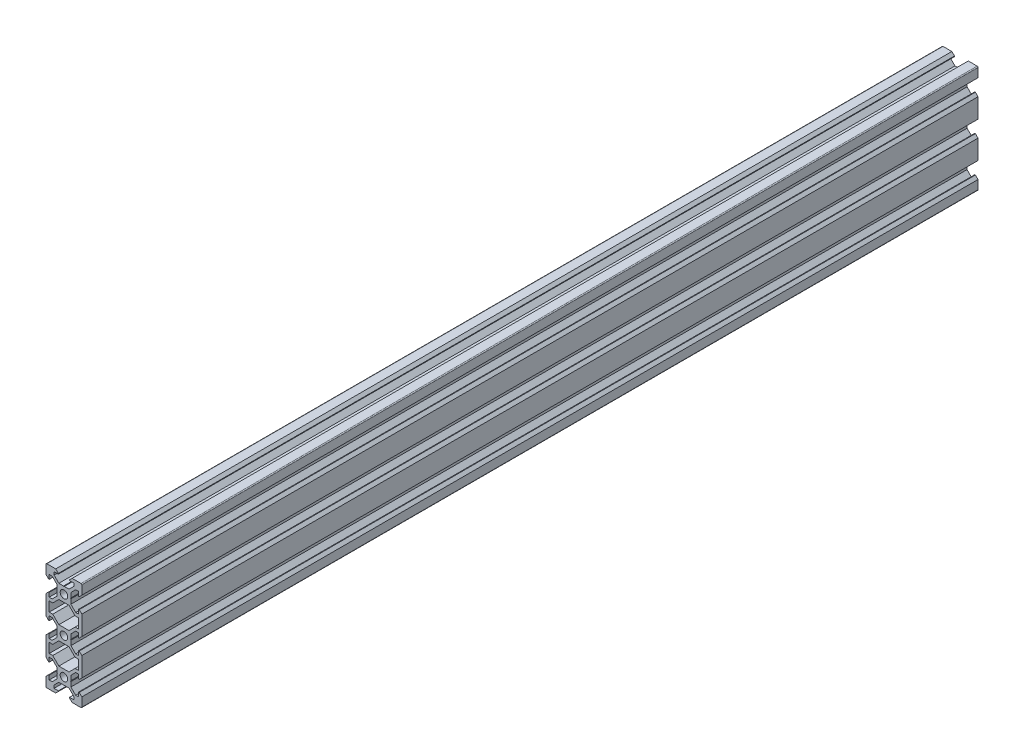
SolidWorks part; units mm, degrees
ref_plane "Front Plane" through (0, 0, 0) normal (0, 0, 1) x (1, 0, 0)
ref_plane "Top Plane" through (0, 0, 0) normal (0, 1, 0) x (1, 0, 0)
ref_plane "Right Plane" through (0, 0, 0) normal (1, 0, 0) x (0, 0, -1)
sketch "Sketch1" plane through (0, 0, 0) normal (0, 0, 1) x (1, 0, 0)
  line B0 (-8.2, -32.7) -> (-6.2393, -32.7)
  line B1 (-6.2393, -32.7) -> (-2.8393, -36.1)
  line B2 (-2.8393, -36.1) -> (2.8393, -36.1)
  line B3 (6.2393, -32.7) -> (2.8393, -36.1)
  line B4 (8.2, -32.7) -> (6.2393, -32.7)
  line B5 (8.2, -32.7) -> (8.2, -27.3)
  line B6 (8.2, -27.3) -> (6.2393, -27.3)
  line B7 (6.2393, -27.3) -> (2.8393, -23.9)
  line B8 (-2.8393, -23.9) -> (2.8393, -23.9)
  line B9 (-6.2393, -27.3) -> (-2.8393, -23.9)
  line B10 (-8.2, -27.3) -> (-6.2393, -27.3)
  line B11 (-8.2, -32.7) -> (-8.2, -27.3)
  line B12 (-8.2, -12.7) -> (-6.2393, -12.7)
  line B13 (-6.2393, -12.7) -> (-2.8393, -16.1)
  line B14 (-2.8393, -16.1) -> (2.8393, -16.1)
  line B15 (6.2393, -12.7) -> (2.8393, -16.1)
  line B16 (8.2, -12.7) -> (6.2393, -12.7)
  line B17 (8.2, -12.7) -> (8.2, -7.3)
  line B18 (8.2, -7.3) -> (6.2393, -7.3)
  line B19 (6.2393, -7.3) -> (2.8393, -3.9)
  line B20 (-2.8393, -3.9) -> (2.8393, -3.9)
  line B21 (-6.2393, -7.3) -> (-2.8393, -3.9)
  line B22 (-8.2, -7.3) -> (-6.2393, -7.3)
  line B23 (-8.2, -12.7) -> (-8.2, -7.3)
  line B24 (3.69, 0) -> (3.9, -0.21)
  line B25 (3.9, -0.21) -> (3.9, -2.8393)
  line B26 (3.9, -2.8393) -> (6.5607, -5.5)
  line B27 (6.5607, -5.5) -> (8.2, -5.5)
  line B28 (8.2, -5.5) -> (8.2, -3.125)
  line B29 (8.2, -3.125) -> (8.545, -3.125)
  line B30 (8.545, -3.125) -> (10, -4.58)
  line B31 (10, -15.42) -> (10, -4.58)
  line B32 (8.545, -16.875) -> (10, -15.42)
  line B33 (8.2, -16.875) -> (8.545, -16.875)
  line B34 (8.2, -14.5) -> (8.2, -16.875)
  line B35 (6.5607, -14.5) -> (8.2, -14.5)
  line B36 (3.9, -17.1607) -> (6.5607, -14.5)
  line B37 (3.9, -19.79) -> (3.9, -17.1607)
  line B38 (3.69, -20) -> (3.9, -19.79)
  line B39 (3.69, -20) -> (3.9, -20.21)
  line B40 (3.9, -20.21) -> (3.9, -22.8393)
  line B41 (3.9, -22.8393) -> (6.5607, -25.5)
  line B42 (6.5607, -25.5) -> (8.2, -25.5)
  line B43 (8.2, -25.5) -> (8.2, -23.125)
  line B44 (8.2, -23.125) -> (8.545, -23.125)
  line B45 (8.545, -23.125) -> (10, -24.58)
  line B46 (10, -35.42) -> (10, -24.58)
  line B47 (8.545, -36.875) -> (10, -35.42)
  line B48 (8.2, -36.875) -> (8.545, -36.875)
  line B49 (8.2, -34.5) -> (8.2, -36.875)
  line B50 (6.5607, -34.5) -> (8.2, -34.5)
  line B51 (3.9, -37.1607) -> (6.5607, -34.5)
  line B52 (3.9, -39.79) -> (3.9, -37.1607)
  line B53 (3.69, -40) -> (3.9, -39.79)
  line B54 (3.69, -40) -> (3.9, -40.21)
  line B55 (3.9, -40.21) -> (3.9, -42.8393)
  line B56 (3.9, -42.8393) -> (6.5607, -45.5)
  line B57 (6.5607, -45.5) -> (8.2, -45.5)
  line B58 (8.2, -45.5) -> (8.2, -43.125)
  line B59 (8.2, -43.125) -> (8.545, -43.125)
  line B60 (8.545, -43.125) -> (10, -44.58)
  line B61 (10, -49.5) -> (10, -44.58)
  arc B62 (9.5, -50) -> (10, -49.5) centre (9.5, -49.5) ccw
  line B63 (9.5, -50) -> (4.58, -50)
  line B64 (3.125, -48.545) -> (4.58, -50)
  line B65 (3.125, -48.2) -> (3.125, -48.545)
  line B66 (5.5, -48.2) -> (3.125, -48.2)
  line B67 (5.5, -46.5607) -> (5.5, -48.2)
  line B68 (2.8393, -43.9) -> (5.5, -46.5607)
  line B69 (0.21, -43.9) -> (2.8393, -43.9)
  line B70 (0, -43.69) -> (0.21, -43.9)
  line B71 (0, -43.69) -> (-0.21, -43.9)
  line B72 (-0.21, -43.9) -> (-2.8393, -43.9)
  line B73 (-2.8393, -43.9) -> (-5.5, -46.5607)
  line B74 (-5.5, -46.5607) -> (-5.5, -48.2)
  line B75 (-5.5, -48.2) -> (-3.125, -48.2)
  line B76 (-3.125, -48.2) -> (-3.125, -48.545)
  line B77 (-3.125, -48.545) -> (-4.58, -50)
  line B78 (-4.58, -50) -> (-9.5, -50)
  arc B79 (-10, -49.5) -> (-9.5, -50) centre (-9.5, -49.5) ccw
  line B80 (-10, -49.5) -> (-10, -44.58)
  line B81 (-8.545, -43.125) -> (-10, -44.58)
  line B82 (-8.2, -43.125) -> (-8.545, -43.125)
  line B83 (-8.2, -45.5) -> (-8.2, -43.125)
  line B84 (-6.5607, -45.5) -> (-8.2, -45.5)
  line B85 (-3.9, -42.8393) -> (-6.5607, -45.5)
  line B86 (-3.9, -40.21) -> (-3.9, -42.8393)
  line B87 (-3.69, -40) -> (-3.9, -40.21)
  line B88 (-3.69, -40) -> (-3.9, -39.79)
  line B89 (-3.9, -39.79) -> (-3.9, -37.1607)
  line B90 (-3.9, -37.1607) -> (-6.5607, -34.5)
  line B91 (-6.5607, -34.5) -> (-8.2, -34.5)
  line B92 (-8.2, -34.5) -> (-8.2, -36.875)
  line B93 (-8.2, -36.875) -> (-8.545, -36.875)
  line B94 (-8.545, -36.875) -> (-10, -35.42)
  line B95 (-10, -35.42) -> (-10, -24.58)
  line B96 (-8.545, -23.125) -> (-10, -24.58)
  line B97 (-8.2, -23.125) -> (-8.545, -23.125)
  line B98 (-8.2, -25.5) -> (-8.2, -23.125)
  line B99 (-6.5607, -25.5) -> (-8.2, -25.5)
  line B100 (-3.9, -22.8393) -> (-6.5607, -25.5)
  line B101 (-3.9, -20.21) -> (-3.9, -22.8393)
  line B102 (-3.69, -20) -> (-3.9, -20.21)
  line B103 (-3.69, -20) -> (-3.9, -19.79)
  line B104 (-3.9, -19.79) -> (-3.9, -17.1607)
  line B105 (-3.9, -17.1607) -> (-6.5607, -14.5)
  line B106 (-6.5607, -14.5) -> (-8.2, -14.5)
  line B107 (-8.2, -14.5) -> (-8.2, -16.875)
  line B108 (-8.2, -16.875) -> (-8.545, -16.875)
  line B109 (-8.545, -16.875) -> (-10, -15.42)
  line B110 (-10, -15.42) -> (-10, -4.58)
  line B111 (-8.545, -3.125) -> (-10, -4.58)
  line B112 (-8.2, -3.125) -> (-8.545, -3.125)
  line B113 (-8.2, -5.5) -> (-8.2, -3.125)
  line B114 (-6.5607, -5.5) -> (-8.2, -5.5)
  line B115 (-3.9, -2.8393) -> (-6.5607, -5.5)
  line B116 (-3.9, -0.21) -> (-3.9, -2.8393)
  line B117 (-3.69, 0) -> (-3.9, -0.21)
  line B118 (-3.69, 0) -> (-3.9, 0.21)
  line B119 (-3.9, 0.21) -> (-3.9, 2.8393)
  line B120 (-3.9, 2.8393) -> (-6.5607, 5.5)
  line B121 (-6.5607, 5.5) -> (-8.2, 5.5)
  line B122 (-8.2, 5.5) -> (-8.2, 3.125)
  line B123 (-8.2, 3.125) -> (-8.545, 3.125)
  line B124 (-8.545, 3.125) -> (-10, 4.58)
  line B125 (-10, 4.58) -> (-10, 9.5)
  arc B126 (-9.5, 10) -> (-10, 9.5) centre (-9.5, 9.5) ccw
  line B127 (-4.58, 10) -> (-9.5, 10)
  line B128 (-3.125, 8.545) -> (-4.58, 10)
  line B129 (-3.125, 8.2) -> (-3.125, 8.545)
  line B130 (-5.5, 8.2) -> (-3.125, 8.2)
  line B131 (-5.5, 6.5607) -> (-5.5, 8.2)
  line B132 (-2.8393, 3.9) -> (-5.5, 6.5607)
  line B133 (-0.21, 3.9) -> (-2.8393, 3.9)
  line B134 (0, 3.69) -> (-0.21, 3.9)
  line B135 (0, 3.69) -> (0.21, 3.9)
  line B136 (0.21, 3.9) -> (2.8393, 3.9)
  line B137 (2.8393, 3.9) -> (5.5, 6.5607)
  line B138 (5.5, 6.5607) -> (5.5, 8.2)
  line B139 (5.5, 8.2) -> (3.125, 8.2)
  line B140 (3.125, 8.2) -> (3.125, 8.545)
  line B141 (3.125, 8.545) -> (4.58, 10)
  line B142 (9.5, 10) -> (4.58, 10)
  arc B143 (10, 9.5) -> (9.5, 10) centre (9.5, 9.5) ccw
  line B144 (10, 4.58) -> (10, 9.5)
  line B145 (8.545, 3.125) -> (10, 4.58)
  line B146 (8.2, 3.125) -> (8.545, 3.125)
  line B147 (8.2, 5.5) -> (8.2, 3.125)
  line B148 (6.5607, 5.5) -> (8.2, 5.5)
  line B149 (3.9, 2.8393) -> (6.5607, 5.5)
  line B150 (3.9, 0.21) -> (3.9, 2.8393)
  line B151 (3.69, 0) -> (3.9, 0.21)
  circle B152 centre (0, -40) radius 2.1
  circle B153 centre (0, -20) radius 2.1
  circle B154 centre (0, 0) radius 2.1
sketch_block_instance "2060 - V-Slot-1"
sketch_block "2060 - V-Slot"
extrude "Boss-Extrude1" add sketch "Sketch1" along normal blind 500
